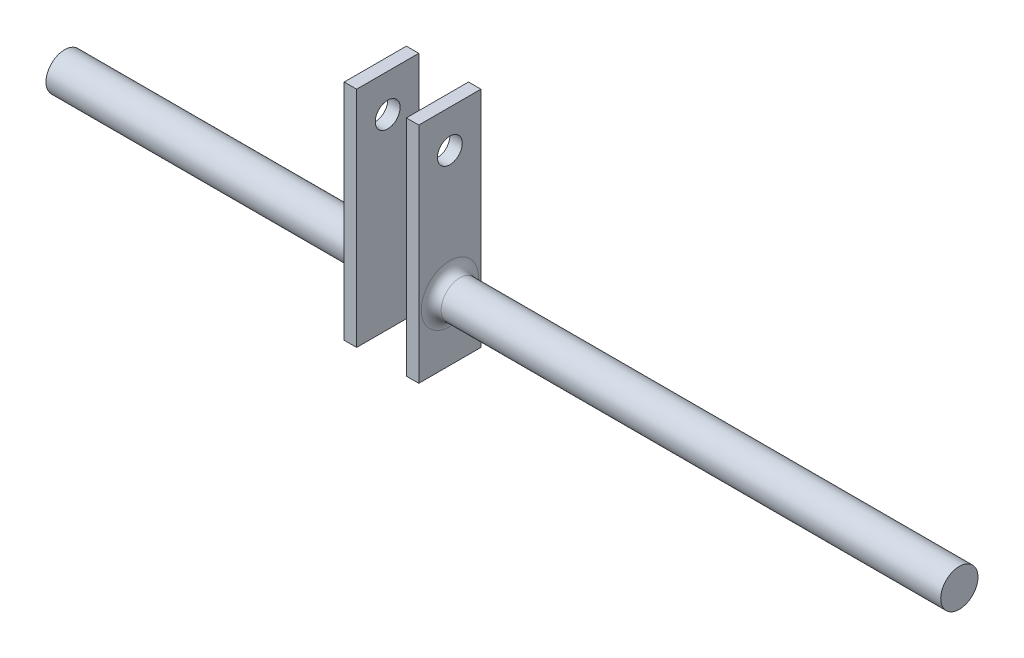
SolidWorks part; units mm, degrees
ref_plane "Front Plane" through (0, 0, 0) normal (0, 0, 1) x (1, 0, 0)
ref_plane "Top Plane" through (0, 0, 0) normal (0, 1, 0) x (1, 0, 0)
ref_plane "Right Plane" through (0, 0, 0) normal (1, 0, 0) x (0, 0, -1)
sketch "Sketch1" plane through (0, 0, 0) normal (1, 0, 0) x (0, 0, -1)
  circle A0 centre (0, 0) radius 7.5
  dimension "D1" = 15
extrude "Boss-Extrude1" add sketch "Sketch1" along normal mid plane 360
sketch "Sketch2" plane through (0, 0, 0) normal (0, 0, 1) x (1, 0, 0)
  line L0 (-180, 7.5) -> (-180, -7.5) construction
  line L1 (-25, 15) -> (-55, 15)
  line L2 (-25, 15) -> (-25, -15)
  line L3 (-25, -15) -> (-55, -15)
  line L4 (-55, 15) -> (-55, -15)
  line L5 (-25, 15) -> (-55, -15) construction
  line L6 (-25, -15) -> (-55, 15) construction
  point P0 (-40, 0)
  dimension "D1" = 155
  dimension "D2" = 30
  dimension "D3" = 30
  dimension "D4" = 0
extrude "Cut-Extrude1" cut sketch "Sketch2" along normal mid plane 360
sketch "Sketch4" plane through (-25, 0, 0) normal (-1, 0, 0) x (0, 0, 1)
  line L1 (-12.5, 65) -> (12.5, 65)
  line L2 (-12.5, 65) -> (-12.5, -25)
  line L3 (-12.5, -25) -> (12.5, -25)
  line L4 (12.5, 65) -> (12.5, -25)
  point P4 (0, -25)
  dimension "D1" = 0
  dimension "D2" = 90
  dimension "D3" = 25
  dimension "D4" = 25
  dimension "D5" = 12.5
extrude "Boss-Extrude2" add sketch "Sketch4" along normal blind 5
sketch "Sketch5" plane through (-55, 0, 0) normal (1, 0, 0) x (0, 0, -1)
  line L0 (12.5, -25) -> (-12.5, -25) construction
  line L1 (-12.5, 65) -> (12.5, 65)
  line L2 (-12.5, 65) -> (-12.5, -25)
  line L3 (-12.5, -25) -> (12.5, -25)
  line L4 (12.5, 65) -> (12.5, -25)
  dimension "D1" = 25
extrude "Boss-Extrude3" add sketch "Sketch5" along normal blind 5
sketch "Sketch6" plane through (-55, 0, 0) normal (-1, 0, 0) x (0, 0, 1)
  line L0 (-12.5, -25) -> (-12.5, 65) construction
  circle A0 centre (0, 49.9099) radius 5
  point P2 (0, 0)
  dimension "D1" = 10
  dimension "D3" = 12.5
extrude "Cut-Extrude2" cut sketch "Sketch6" against normal through all both and the other way through all
fillet "Fillet1" radius 4 1 edges at (-55, 7.5, 0)
fillet "Fillet2" radius 4 1 edges at (-25, 0, 7.5)
